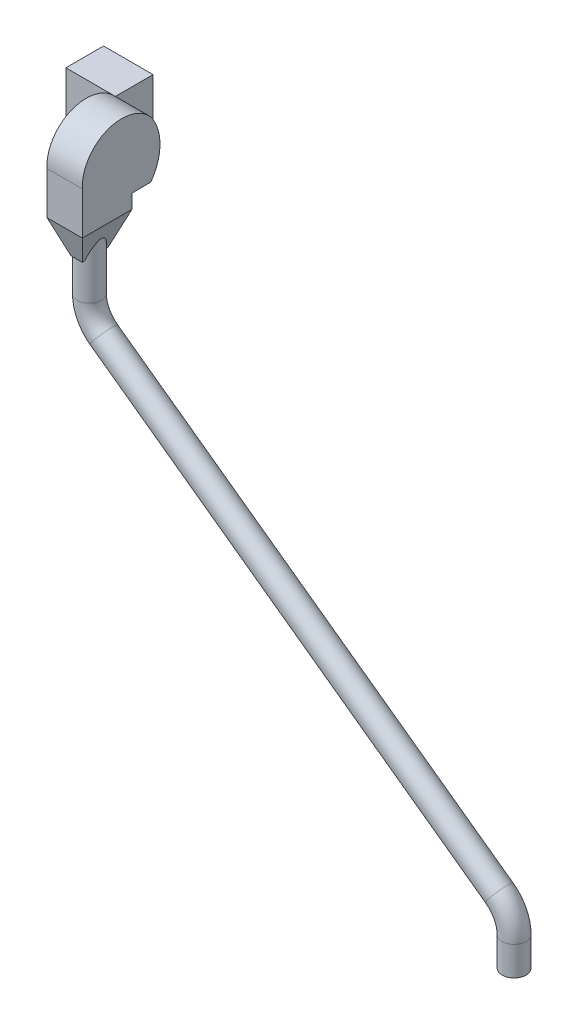
SolidWorks part; units mm, degrees
ref_plane "Alzado" through (0, 0, 0) normal (0, 0, 1) x (1, 0, 0)
ref_plane "Planta" through (0, 0, 0) normal (0, 1, 0) x (1, 0, 0)
ref_plane "Vista lateral" through (0, 0, 0) normal (1, 0, 0) x (0, 0, -1)
sketch "Croquis1" plane through (0, 0, 0) normal (0, 0, 1) x (1, 0, 0)
  line L1 (-105, -120) -> (105, -120)
  line L2 (-105, -120) -> (-105, 120)
  line L3 (-105, 120) -> (105, 120)
  line L4 (105, -120) -> (105, 120)
  line L5 (-105, -120) -> (105, 120) construction
  line L6 (-105, 120) -> (105, -120) construction
  point P0 (0, 0)
  dimension "D1" = 210
  dimension "D2" = 240
extrude "Saliente-Extruir1" add sketch "Croquis1" along normal blind 160
sketch "Croquis2" plane through (105, 0, 0) normal (1, 0, 0) x (0, 0, -1)
  line L0 (-160, -120) -> (-450, -120)
  line L1 (-450, -120) -> (-450, 0)
  arc A0 (-450, 0) -> (-160, 120) centre (-283.7057, 8.5387) cw
  arc A1 (-160, -120) -> (-160, 120) centre (-324.1232, 0) ccw
  dimension "D1" = 450
extrude "Saliente-Extruir2" add sketch "Croquis2" along normal blind 150 separate body
sketch "Croquis3" plane through (0, -120, 0) normal (0, -1, 0) x (1, 0, 0)
  line L0 (105, 450) -> (255, 450)
  line L1 (255, 450) -> (255, 239.8579)
  line L2 (255, 450) -> (255, 160) construction
  line L3 (255, 239.8579) -> (105, 239.8579)
  line L4 (105, 450) -> (105, 160) construction
  line L5 (105, 239.8579) -> (105, 450)
extrude "Saliente-Extruir3" add sketch "Croquis3" along normal blind 60
sketch "Croquis4" plane through (0, -180, 0) normal (0, -1, 0) x (1, 0, 0)
  circle A0 centre (180, 344.9289) radius 50.8
  dimension "D1" = 101.6
extrude "Saliente-Extruir4" add sketch "Croquis4" along normal blind 170
sketch "Croquis5" plane through (0, -180, 0) normal (0, -1, 0) x (1, 0, 0)
  line L0 (105, 450) -> (255, 450)
  line L1 (255, 450) -> (255, 239.8579)
  line L2 (255, 239.8579) -> (105, 239.8579)
  line L3 (105, 239.8579) -> (105, 450)
extrude "Saliente-Extruir5" add sketch "Croquis5" along normal blind 140 draft 20
sketch3d "Croquis3D1"
  line L0 (180, -350, 344.9289) -> (180, -2050, 344.9289) construction
  line L3 (180, -350, 344.9289) -> (180, -320, 344.9289) construction
  line L4 (180, -2050, 344.9289) -> (1980, -2050, 344.9289) construction
  line L5 (1980, -2050, 344.9289) -> (1980, -1926.6967, 344.9289)
  line L6 (1917.8236, -1805.0948, 344.9289) -> (242.1764, -594.9052, 344.9289)
  line L7 (180, -473.3033, 344.9289) -> (180, -350, 344.9289)
  arc A0 (242.1764, -594.9052, 344.9289) -> (180, -473.3033, 344.9289) centre (330, -473.3033, 344.9289) ccw
  arc A1 (1980, -1926.6967, 344.9289) -> (1917.8236, -1805.0948, 344.9289) centre (1830, -1926.6967, 344.9289) ccw
  point P9 (180, -550, 344.9289)
  point P10 (330, -473.3033, 194.9289)
  point P13 (1980, -1850, 344.9289)
  point P14 (1830, -1926.6967, 494.9289)
  dimension "D5" = 150
  dimension "D6" = 150
  dimension "D1" = 1700
  dimension "D3" = 200
  dimension "D2" = 1800
  dimension "D4" = 200
sketch "Croquis7" plane through (0, -350, 0) normal (0, -1, 0) x (1, 0, 0)
  circle A0 centre (180, 344.9289) radius 50.8
sweep "Barrer1" add profiles "Croquis7" path "Croquis3D1"
